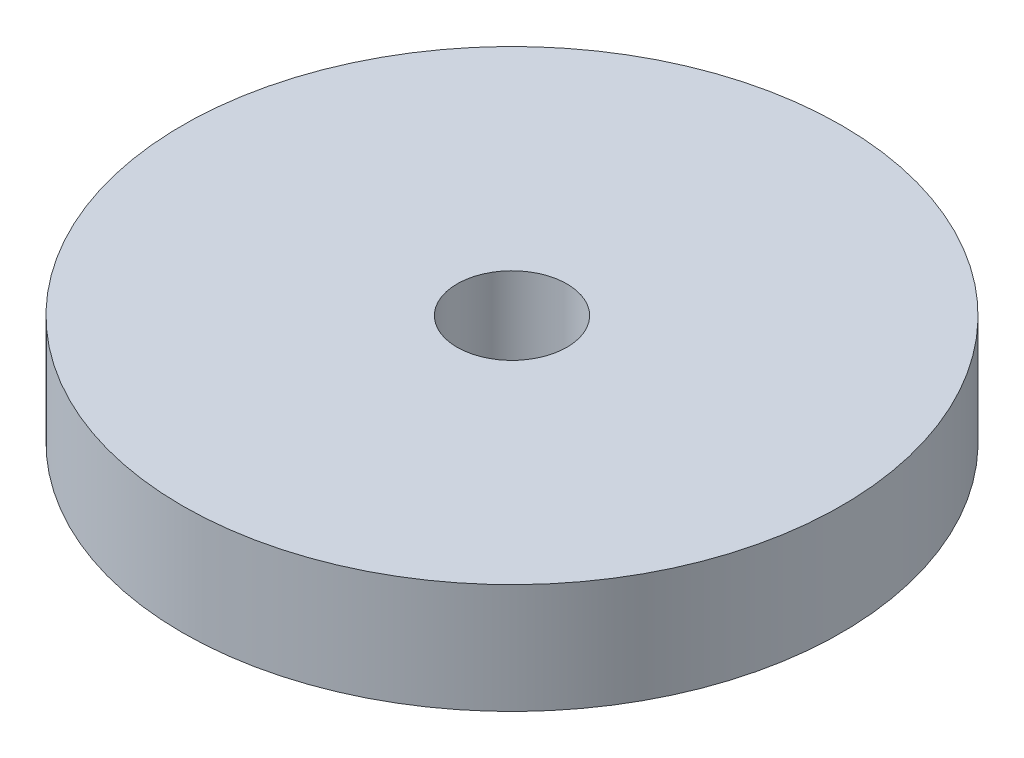
SolidWorks part; units mm, degrees
material "Neodymium"
ref_plane "Front Plane" through (0, 0, 0) normal (0, 0, 1) x (1, 0, 0)
ref_plane "Top Plane" through (0, 0, 0) normal (0, 1, 0) x (1, 0, 0)
ref_plane "Right Plane" through (0, 0, 0) normal (1, 0, 0) x (0, 0, -1)
other "Neodynium"
sketch "Sketch1" plane through (0, 0, 0) normal (0, 1, 0) x (1, 0, 0)
  circle A0 centre (0, 0) radius 9.525
  circle A1 centre (0, 0) radius 1.5875
  dimension "D1" = 3.175
  dimension "D2" = 19.05
extrude "Boss-Extrude1" add sketch "Sketch1" along normal blind 3.175
